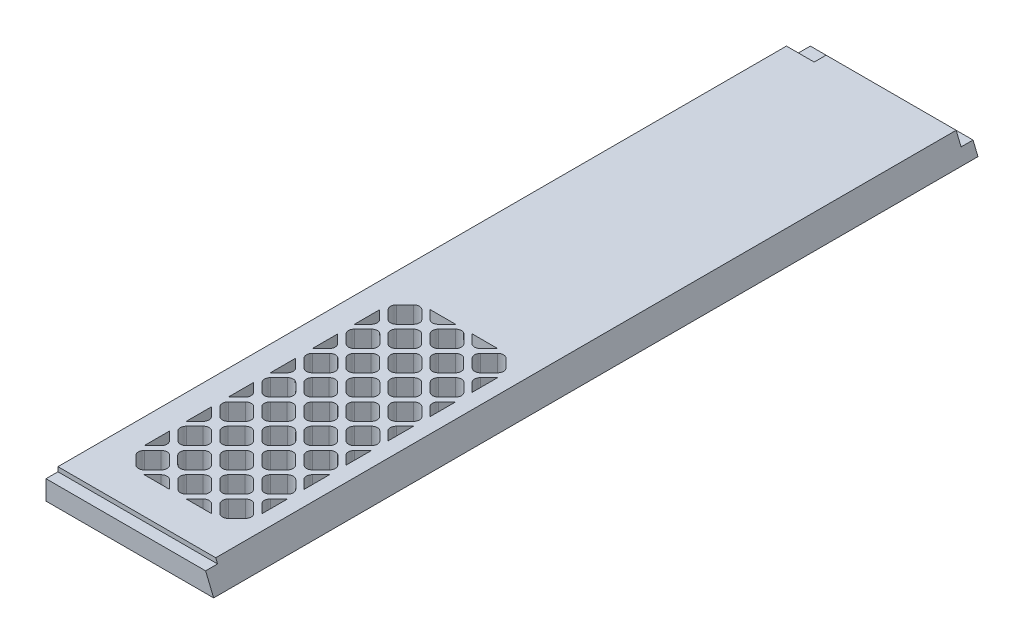
SolidWorks part; units mm, degrees
ref_plane "Front Plane" through (0, 0, 0) normal (0, 0, 1) x (1, 0, 0)
ref_plane "Top Plane" through (0, 0, 0) normal (0, 1, 0) x (1, 0, 0)
ref_plane "Right Plane" through (0, 0, 0) normal (1, 0, 0) x (0, 0, -1)
sketch "Sketch1" plane through (0, 0, 0) normal (0, 0, 1) x (1, 0, 0)
  line L0 (0, 0) -> (0, 12.7)
  line L1 (0, 12.7) -> (83.8935, 12.7)
  line L2 (83.8935, 12.7) -> (89.154, 0)
  line L3 (89.154, 0) -> (0, 0)
  dimension "D1" = 12.7
  dimension "D2" = 67.5
  dimension "D3" = 89.154
extrude "Boss-Extrude1" add sketch "Sketch1" along normal blind 406.4
sketch "Sketch2" plane through (0, 12.7, 0) normal (0, -1, 0) x (1, 0, 0)
  line L5 (89.154, 406.4) -> (89.154, 0) construction
  line L6 (0, 406.4) -> (89.154, 406.4)
  line L7 (0, 406.4) -> (0, 400.05)
  line L8 (0, 400.05) -> (89.154, 400.05)
  line L9 (89.154, 406.4) -> (89.154, 400.05)
  dimension "D1" = 6.35
extrude "Cut-Extrude1" cut sketch "Sketch2" along normal blind 2.3622
sketch "Sketch3" plane through (0, 0, 0) normal (0, -1, 0) x (1, 0, 0)
  line L0 (15.4898, 374.1011) -> (19.9799, 378.5912)
  line L1 (13.2447, 380.8363) -> (75.9093, 380.8363)
  line L2 (13.2447, 380.8363) -> (13.2447, 228.7637)
  line L3 (13.2447, 228.7637) -> (75.9093, 228.7637)
  line L4 (75.9093, 380.8363) -> (75.9093, 228.7637)
  line L5 (24.4701, 378.5912) -> (28.9602, 374.1011)
  line L6 (28.9602, 369.6109) -> (24.4701, 365.1208)
  line L7 (19.9799, 365.1208) -> (15.4898, 369.6109)
  line L8 (42.3319, 365.1208) -> (37.8418, 369.6109)
  line L9 (37.8418, 374.1011) -> (42.3319, 378.5912)
  line L10 (46.8221, 378.5912) -> (51.3122, 374.1011)
  line L11 (51.3122, 369.6109) -> (46.8221, 365.1208)
  line L12 (64.6839, 365.1208) -> (60.1938, 369.6109)
  line L13 (60.1938, 374.1011) -> (64.6839, 378.5912)
  line L14 (69.1741, 378.5912) -> (73.6642, 374.1011)
  line L15 (73.6642, 369.6109) -> (69.1741, 365.1208)
  line L16 (19.9799, 342.7688) -> (15.4898, 347.2589)
  line L17 (15.4898, 351.7491) -> (19.9799, 356.2392)
  line L18 (24.4701, 356.2392) -> (28.9602, 351.7491)
  line L19 (28.9602, 347.2589) -> (24.4701, 342.7688)
  line L20 (42.3319, 342.7688) -> (37.8418, 347.2589)
  line L21 (37.8418, 351.7491) -> (42.3319, 356.2392)
  line L22 (46.8221, 356.2392) -> (51.3122, 351.7491)
  line L23 (51.3122, 347.2589) -> (46.8221, 342.7688)
  line L24 (64.6839, 342.7688) -> (60.1938, 347.2589)
  line L25 (60.1938, 351.7491) -> (64.6839, 356.2392)
  line L26 (69.1741, 356.2392) -> (73.6642, 351.7491)
  line L27 (73.6642, 347.2589) -> (69.1741, 342.7688)
  line L28 (19.9799, 320.4168) -> (15.4898, 324.9069)
  line L29 (15.4898, 329.3971) -> (19.9799, 333.8872)
  line L30 (24.4701, 333.8872) -> (28.9602, 329.3971)
  line L31 (28.9602, 324.9069) -> (24.4701, 320.4168)
  line L32 (42.3319, 320.4168) -> (37.8418, 324.9069)
  line L33 (37.8418, 329.3971) -> (42.3319, 333.8872)
  line L34 (46.8221, 333.8872) -> (51.3122, 329.3971)
  line L35 (51.3122, 324.9069) -> (46.8221, 320.4168)
  line L36 (64.6839, 320.4168) -> (60.1938, 324.9069)
  line L37 (60.1938, 329.3971) -> (64.6839, 333.8872)
  line L38 (69.1741, 333.8872) -> (73.6642, 329.3971)
  line L39 (73.6642, 324.9069) -> (69.1741, 320.4168)
  line L40 (19.9799, 298.0648) -> (15.4898, 302.5549)
  line L41 (15.4898, 307.0451) -> (19.9799, 311.5352)
  line L42 (24.4701, 311.5352) -> (28.9602, 307.0451)
  line L43 (28.9602, 302.5549) -> (24.4701, 298.0648)
  line L44 (42.3319, 298.0648) -> (37.8418, 302.5549)
  line L45 (37.8418, 307.0451) -> (42.3319, 311.5352)
  line L46 (46.8221, 311.5352) -> (51.3122, 307.0451)
  line L47 (51.3122, 302.5549) -> (46.8221, 298.0648)
  line L48 (64.6839, 298.0648) -> (60.1938, 302.5549)
  line L49 (60.1938, 307.0451) -> (64.6839, 311.5352)
  line L50 (69.1741, 311.5352) -> (73.6642, 307.0451)
  line L51 (73.6642, 302.5549) -> (69.1741, 298.0648)
  line L52 (19.9799, 275.7128) -> (15.4898, 280.2029)
  line L53 (15.4898, 284.6931) -> (19.9799, 289.1832)
  line L54 (24.4701, 289.1832) -> (28.9602, 284.6931)
  line L55 (28.9602, 280.2029) -> (24.4701, 275.7128)
  line L56 (42.3319, 275.7128) -> (37.8418, 280.2029)
  line L57 (37.8418, 284.6931) -> (42.3319, 289.1832)
  line L58 (46.8221, 289.1832) -> (51.3122, 284.6931)
  line L59 (51.3122, 280.2029) -> (46.8221, 275.7128)
  line L60 (64.6839, 275.7128) -> (60.1938, 280.2029)
  line L61 (60.1938, 284.6931) -> (64.6839, 289.1832)
  line L62 (69.1741, 289.1832) -> (73.6642, 284.6931)
  line L63 (73.6642, 280.2029) -> (69.1741, 275.7128)
  line L64 (19.9799, 253.3608) -> (15.4898, 257.8509)
  line L65 (15.4898, 262.3411) -> (19.9799, 266.8312)
  line L66 (24.4701, 266.8312) -> (28.9602, 262.3411)
  line L67 (28.9602, 257.8509) -> (24.4701, 253.3608)
  line L68 (42.3319, 253.3608) -> (37.8418, 257.8509)
  line L69 (37.8418, 262.3411) -> (42.3319, 266.8312)
  line L70 (46.8221, 266.8312) -> (51.3122, 262.3411)
  line L71 (51.3122, 257.8509) -> (46.8221, 253.3608)
  line L72 (64.6839, 253.3608) -> (60.1938, 257.8509)
  line L73 (60.1938, 262.3411) -> (64.6839, 266.8312)
  line L74 (69.1741, 266.8312) -> (73.6642, 262.3411)
  line L75 (73.6642, 257.8509) -> (69.1741, 253.3608)
  line L76 (19.9799, 231.0088) -> (15.4898, 235.4989)
  line L77 (15.4898, 239.9891) -> (19.9799, 244.4792)
  line L78 (24.4701, 244.4792) -> (28.9602, 239.9891)
  line L79 (28.9602, 235.4989) -> (24.4701, 231.0088)
  line L80 (42.3319, 231.0088) -> (37.8418, 235.4989)
  line L81 (37.8418, 239.9891) -> (42.3319, 244.4792)
  line L82 (46.8221, 244.4792) -> (51.3122, 239.9891)
  line L83 (51.3122, 235.4989) -> (46.8221, 231.0088)
  line L84 (64.6839, 231.0088) -> (60.1938, 235.4989)
  line L85 (60.1938, 239.9891) -> (64.6839, 244.4792)
  line L86 (69.1741, 244.4792) -> (73.6642, 239.9891)
  line L87 (73.6642, 235.4989) -> (69.1741, 231.0088)
  line L91 (0, 400.05) -> (89.154, 400.05) construction
  line L92 (13.2447, 376.3461) -> (17.7349, 380.8363)
  line L98 (35.5967, 376.3461) -> (40.0869, 380.8363)
  line L99 (31.1066, 376.3461) -> (26.6165, 380.8363)
  line L102 (57.9487, 376.3461) -> (62.4389, 380.8363)
  line L103 (53.4586, 376.3461) -> (48.9685, 380.8363)
  line L107 (75.8106, 376.3461) -> (71.3205, 380.8363)
  line L108 (26.6165, 362.9744) -> (31.1066, 367.4645)
  line L109 (40.0869, 362.9744) -> (35.5967, 367.4645)
  line L110 (35.5967, 353.9941) -> (40.0869, 358.4843)
  line L111 (31.1066, 353.9941) -> (26.6165, 358.4843)
  line L112 (48.9685, 362.9744) -> (53.4586, 367.4645)
  line L113 (62.4389, 362.9744) -> (57.9487, 367.4645)
  line L114 (57.9487, 353.9941) -> (62.4389, 358.4843)
  line L115 (53.4586, 353.9941) -> (48.9685, 358.4843)
  line L116 (71.3205, 362.9744) -> (75.8106, 367.4645)
  line L119 (75.8106, 353.9941) -> (71.3205, 358.4843)
  line L120 (26.6165, 340.6224) -> (31.1066, 345.1125)
  line L121 (40.0869, 340.6224) -> (35.5967, 345.1125)
  line L122 (35.5967, 331.6421) -> (40.0869, 336.1323)
  line L123 (31.1066, 331.6421) -> (26.6165, 336.1323)
  line L124 (48.9685, 340.6224) -> (53.4586, 345.1125)
  line L125 (62.4389, 340.6224) -> (57.9487, 345.1125)
  line L126 (57.9487, 331.6421) -> (62.4389, 336.1323)
  line L127 (53.4586, 331.6421) -> (48.9685, 336.1323)
  line L128 (71.3205, 340.6224) -> (75.8106, 345.1125)
  line L131 (75.8106, 331.6421) -> (71.3205, 336.1323)
  line L132 (26.6165, 318.2704) -> (31.1066, 322.7605)
  line L133 (40.0869, 318.2704) -> (35.5967, 322.7605)
  line L134 (35.5967, 309.2901) -> (40.0869, 313.7803)
  line L135 (31.1066, 309.2901) -> (26.6165, 313.7803)
  line L136 (48.9685, 318.2704) -> (53.4586, 322.7605)
  line L137 (62.4389, 318.2704) -> (57.9487, 322.7605)
  line L138 (57.9487, 309.2901) -> (62.4389, 313.7803)
  line L139 (53.4586, 309.2901) -> (48.9685, 313.7803)
  line L140 (71.3205, 318.2704) -> (75.8106, 322.7605)
  line L143 (75.8106, 309.2901) -> (71.3205, 313.7803)
  line L144 (26.6165, 295.9184) -> (31.1066, 300.4085)
  line L145 (40.0869, 295.9184) -> (35.5967, 300.4085)
  line L146 (35.5967, 286.9381) -> (40.0869, 291.4283)
  line L147 (31.1066, 286.9381) -> (26.6165, 291.4283)
  line L148 (48.9685, 295.9184) -> (53.4586, 300.4085)
  line L149 (62.4389, 295.9184) -> (57.9487, 300.4085)
  line L150 (57.9487, 286.9381) -> (62.4389, 291.4283)
  line L151 (53.4586, 286.9381) -> (48.9685, 291.4283)
  line L152 (71.3205, 295.9184) -> (75.8106, 300.4085)
  line L155 (75.8106, 286.9381) -> (71.3205, 291.4283)
  line L156 (26.6165, 273.5664) -> (31.1066, 278.0565)
  line L157 (40.0869, 273.5664) -> (35.5967, 278.0565)
  line L158 (35.5967, 264.5861) -> (40.0869, 269.0763)
  line L159 (31.1066, 264.5861) -> (26.6165, 269.0763)
  line L160 (48.9685, 273.5664) -> (53.4586, 278.0565)
  line L161 (62.4389, 273.5664) -> (57.9487, 278.0565)
  line L162 (57.9487, 264.5861) -> (62.4389, 269.0763)
  line L163 (53.4586, 264.5861) -> (48.9685, 269.0763)
  line L164 (71.3205, 273.5664) -> (75.8106, 278.0565)
  line L167 (75.8106, 264.5861) -> (71.3205, 269.0763)
  line L168 (26.6165, 251.2144) -> (31.1066, 255.7045)
  line L169 (40.0869, 251.2144) -> (35.5967, 255.7045)
  line L170 (35.5967, 242.2341) -> (40.0869, 246.7243)
  line L171 (31.1066, 242.2341) -> (26.6165, 246.7243)
  line L172 (48.9685, 251.2144) -> (53.4586, 255.7045)
  line L173 (62.4389, 251.2144) -> (57.9487, 255.7045)
  line L174 (57.9487, 242.2341) -> (62.4389, 246.7243)
  line L175 (53.4586, 242.2341) -> (48.9685, 246.7243)
  line L176 (71.3205, 251.2144) -> (75.8106, 255.7045)
  line L179 (75.8106, 242.2341) -> (71.3205, 246.7243)
  line L180 (26.6165, 228.8624) -> (31.1066, 233.3525)
  line L181 (40.0869, 228.8624) -> (35.5967, 233.3525)
  line L184 (48.9685, 228.8624) -> (53.4586, 233.3525)
  line L185 (62.4389, 228.8624) -> (57.9487, 233.3525)
  line L188 (71.3205, 228.8624) -> (75.8106, 233.3525)
  line L193 (17.7349, 362.9744) -> (13.2447, 367.4645)
  line L194 (13.2447, 353.9941) -> (17.7349, 358.4843)
  line L197 (17.7349, 340.6224) -> (13.2447, 345.1125)
  line L198 (13.2447, 331.6421) -> (17.7349, 336.1323)
  line L201 (17.7349, 318.2704) -> (13.2447, 322.7605)
  line L202 (13.2447, 309.2901) -> (17.7349, 313.7803)
  line L205 (17.7349, 295.9184) -> (13.2447, 300.4085)
  line L206 (13.2447, 286.9381) -> (17.7349, 291.4283)
  line L209 (17.7349, 273.5664) -> (13.2447, 278.0565)
  line L210 (13.2447, 264.5861) -> (17.7349, 269.0763)
  line L213 (17.7349, 251.2144) -> (13.2447, 255.7045)
  line L214 (13.2447, 242.2341) -> (17.7349, 246.7243)
  line L217 (17.7349, 228.8624) -> (13.2447, 233.3525)
  line L220 (80.3007, 376.3461) -> (84.7909, 380.8363) [skipped]
  line L221 (80.3007, 353.9941) -> (84.7909, 358.4843) [skipped]
  line L222 (80.3007, 331.6421) -> (84.7909, 336.1323) [skipped]
  line L223 (80.3007, 309.2901) -> (84.7909, 313.7803) [skipped]
  line L224 (80.3007, 286.9381) -> (84.7909, 291.4283) [skipped]
  line L225 (80.3007, 264.5861) -> (84.7909, 269.0763) [skipped]
  line L226 (80.3007, 242.2341) -> (84.7909, 246.7243) [skipped]
  line L227 (80.3007, 219.8821) -> (84.7909, 224.3723) [skipped]
  line L228 (57.9487, 219.8821) -> (62.4389, 224.3723) [skipped]
  line L229 (35.5967, 219.8821) -> (40.0869, 224.3723) [skipped]
  line L230 (13.2447, 219.8821) -> (17.7349, 224.3723) [skipped]
  arc A0 (24.4701, 365.1208) -> (19.9799, 365.1208) centre (22.225, 367.3659) cw
  arc A1 (28.9602, 374.1011) -> (28.9602, 369.6109) centre (26.7151, 371.856) cw
  arc A2 (15.4898, 374.1011) -> (15.4898, 369.6109) centre (17.7349, 371.856) ccw
  arc A3 (19.9799, 378.5912) -> (24.4701, 378.5912) centre (22.225, 376.3461) cw
  arc A4 (37.8418, 374.1011) -> (37.8418, 369.6109) centre (40.0869, 371.856) ccw
  arc A5 (46.8221, 365.1208) -> (42.3319, 365.1208) centre (44.577, 367.3659) cw
  arc A6 (42.3319, 378.5912) -> (46.8221, 378.5912) centre (44.577, 376.3461) cw
  arc A7 (51.3122, 374.1011) -> (51.3122, 369.6109) centre (49.0671, 371.856) cw
  arc A8 (60.1938, 374.1011) -> (60.1938, 369.6109) centre (62.4389, 371.856) ccw
  arc A9 (69.1741, 365.1208) -> (64.6839, 365.1208) centre (66.929, 367.3659) cw
  arc A10 (64.6839, 378.5912) -> (69.1741, 378.5912) centre (66.929, 376.3461) cw
  arc A11 (73.6642, 374.1011) -> (73.6642, 369.6109) centre (71.4191, 371.856) cw
  arc A12 (15.4898, 351.7491) -> (15.4898, 347.2589) centre (17.7349, 349.504) ccw
  arc A13 (24.4701, 342.7688) -> (19.9799, 342.7688) centre (22.225, 345.0139) cw
  arc A14 (19.9799, 356.2392) -> (24.4701, 356.2392) centre (22.225, 353.9941) cw
  arc A15 (28.9602, 351.7491) -> (28.9602, 347.2589) centre (26.7151, 349.504) cw
  arc A16 (37.8418, 351.7491) -> (37.8418, 347.2589) centre (40.0869, 349.504) ccw
  arc A17 (42.3319, 356.2392) -> (46.8221, 356.2392) centre (44.577, 353.9941) cw
  arc A18 (51.3122, 351.7491) -> (51.3122, 347.2589) centre (49.0671, 349.504) cw
  arc A19 (46.8221, 342.7688) -> (42.3319, 342.7688) centre (44.577, 345.0139) cw
  arc A20 (60.1938, 351.7491) -> (60.1938, 347.2589) centre (62.4389, 349.504) ccw
  arc A21 (64.6839, 356.2392) -> (69.1741, 356.2392) centre (66.929, 353.9941) cw
  arc A22 (73.6642, 351.7491) -> (73.6642, 347.2589) centre (71.4191, 349.504) cw
  arc A23 (69.1741, 342.7688) -> (64.6839, 342.7688) centre (66.929, 345.0139) cw
  arc A24 (15.4898, 329.3971) -> (15.4898, 324.9069) centre (17.7349, 327.152) ccw
  arc A25 (24.4701, 320.4168) -> (19.9799, 320.4168) centre (22.225, 322.6619) cw
  arc A26 (19.9799, 333.8872) -> (24.4701, 333.8872) centre (22.225, 331.6421) cw
  arc A27 (28.9602, 329.3971) -> (28.9602, 324.9069) centre (26.7151, 327.152) cw
  arc A28 (37.8418, 329.3971) -> (37.8418, 324.9069) centre (40.0869, 327.152) ccw
  arc A29 (42.3319, 333.8872) -> (46.8221, 333.8872) centre (44.577, 331.6421) cw
  arc A30 (51.3122, 329.3971) -> (51.3122, 324.9069) centre (49.0671, 327.152) cw
  arc A31 (46.8221, 320.4168) -> (42.3319, 320.4168) centre (44.577, 322.6619) cw
  arc A32 (60.1938, 329.3971) -> (60.1938, 324.9069) centre (62.4389, 327.152) ccw
  arc A33 (64.6839, 333.8872) -> (69.1741, 333.8872) centre (66.929, 331.6421) cw
  arc A34 (73.6642, 329.3971) -> (73.6642, 324.9069) centre (71.4191, 327.152) cw
  arc A35 (69.1741, 320.4168) -> (64.6839, 320.4168) centre (66.929, 322.6619) cw
  arc A36 (15.4898, 307.0451) -> (15.4898, 302.5549) centre (17.7349, 304.8) ccw
  arc A37 (24.4701, 298.0648) -> (19.9799, 298.0648) centre (22.225, 300.3099) cw
  arc A38 (19.9799, 311.5352) -> (24.4701, 311.5352) centre (22.225, 309.2901) cw
  arc A39 (28.9602, 307.0451) -> (28.9602, 302.5549) centre (26.7151, 304.8) cw
  arc A40 (37.8418, 307.0451) -> (37.8418, 302.5549) centre (40.0869, 304.8) ccw
  arc A41 (42.3319, 311.5352) -> (46.8221, 311.5352) centre (44.577, 309.2901) cw
  arc A42 (51.3122, 307.0451) -> (51.3122, 302.5549) centre (49.0671, 304.8) cw
  arc A43 (46.8221, 298.0648) -> (42.3319, 298.0648) centre (44.577, 300.3099) cw
  arc A44 (60.1938, 307.0451) -> (60.1938, 302.5549) centre (62.4389, 304.8) ccw
  arc A45 (64.6839, 311.5352) -> (69.1741, 311.5352) centre (66.929, 309.2901) cw
  arc A46 (73.6642, 307.0451) -> (73.6642, 302.5549) centre (71.4191, 304.8) cw
  arc A47 (69.1741, 298.0648) -> (64.6839, 298.0648) centre (66.929, 300.3099) cw
  arc A48 (15.4898, 284.6931) -> (15.4898, 280.2029) centre (17.7349, 282.448) ccw
  arc A49 (24.4701, 275.7128) -> (19.9799, 275.7128) centre (22.225, 277.9579) cw
  arc A50 (19.9799, 289.1832) -> (24.4701, 289.1832) centre (22.225, 286.9381) cw
  arc A51 (28.9602, 284.6931) -> (28.9602, 280.2029) centre (26.7151, 282.448) cw
  arc A52 (37.8418, 284.6931) -> (37.8418, 280.2029) centre (40.0869, 282.448) ccw
  arc A53 (42.3319, 289.1832) -> (46.8221, 289.1832) centre (44.577, 286.9381) cw
  arc A54 (51.3122, 284.6931) -> (51.3122, 280.2029) centre (49.0671, 282.448) cw
  arc A55 (46.8221, 275.7128) -> (42.3319, 275.7128) centre (44.577, 277.9579) cw
  arc A56 (60.1938, 284.6931) -> (60.1938, 280.2029) centre (62.4389, 282.448) ccw
  arc A57 (64.6839, 289.1832) -> (69.1741, 289.1832) centre (66.929, 286.9381) cw
  arc A58 (73.6642, 284.6931) -> (73.6642, 280.2029) centre (71.4191, 282.448) cw
  arc A59 (69.1741, 275.7128) -> (64.6839, 275.7128) centre (66.929, 277.9579) cw
  arc A60 (15.4898, 262.3411) -> (15.4898, 257.8509) centre (17.7349, 260.096) ccw
  arc A61 (24.4701, 253.3608) -> (19.9799, 253.3608) centre (22.225, 255.6059) cw
  arc A62 (19.9799, 266.8312) -> (24.4701, 266.8312) centre (22.225, 264.5861) cw
  arc A63 (28.9602, 262.3411) -> (28.9602, 257.8509) centre (26.7151, 260.096) cw
  arc A64 (37.8418, 262.3411) -> (37.8418, 257.8509) centre (40.0869, 260.096) ccw
  arc A65 (42.3319, 266.8312) -> (46.8221, 266.8312) centre (44.577, 264.5861) cw
  arc A66 (51.3122, 262.3411) -> (51.3122, 257.8509) centre (49.0671, 260.096) cw
  arc A67 (46.8221, 253.3608) -> (42.3319, 253.3608) centre (44.577, 255.6059) cw
  arc A68 (60.1938, 262.3411) -> (60.1938, 257.8509) centre (62.4389, 260.096) ccw
  arc A69 (64.6839, 266.8312) -> (69.1741, 266.8312) centre (66.929, 264.5861) cw
  arc A70 (73.6642, 262.3411) -> (73.6642, 257.8509) centre (71.4191, 260.096) cw
  arc A71 (69.1741, 253.3608) -> (64.6839, 253.3608) centre (66.929, 255.6059) cw
  arc A72 (15.4898, 239.9891) -> (15.4898, 235.4989) centre (17.7349, 237.744) ccw
  arc A73 (24.4701, 231.0088) -> (19.9799, 231.0088) centre (22.225, 233.2539) cw
  arc A74 (19.9799, 244.4792) -> (24.4701, 244.4792) centre (22.225, 242.2341) cw
  arc A75 (28.9602, 239.9891) -> (28.9602, 235.4989) centre (26.7151, 237.744) cw
  arc A76 (37.8418, 239.9891) -> (37.8418, 235.4989) centre (40.0869, 237.744) ccw
  arc A77 (42.3319, 244.4792) -> (46.8221, 244.4792) centre (44.577, 242.2341) cw
  arc A78 (51.3122, 239.9891) -> (51.3122, 235.4989) centre (49.0671, 237.744) cw
  arc A79 (46.8221, 231.0088) -> (42.3319, 231.0088) centre (44.577, 233.2539) cw
  arc A80 (60.1938, 239.9891) -> (60.1938, 235.4989) centre (62.4389, 237.744) ccw
  arc A81 (64.6839, 244.4792) -> (69.1741, 244.4792) centre (66.929, 242.2341) cw
  arc A82 (73.6642, 239.9891) -> (73.6642, 235.4989) centre (71.4191, 237.744) cw
  arc A83 (69.1741, 231.0088) -> (64.6839, 231.0088) centre (66.929, 233.2539) cw
  arc A91 (35.5967, 376.3461) -> (31.1066, 376.3461) centre (33.3517, 378.5912) cw
  arc A95 (57.9487, 376.3461) -> (53.4586, 376.3461) centre (55.7037, 378.5912) cw
  arc A99 (75.9093, 376.2516) -> (75.8106, 376.3461) centre (78.0557, 378.5912) cw
  arc A100 (35.5967, 367.4645) -> (31.1066, 367.4645) centre (33.3517, 365.2194) ccw
  arc A101 (26.6165, 358.4843) -> (26.6165, 362.9744) centre (28.8616, 360.7293) cw
  arc A102 (40.0869, 358.4843) -> (40.0869, 362.9744) centre (37.8418, 360.7293) ccw
  arc A103 (35.5967, 353.9941) -> (31.1066, 353.9941) centre (33.3517, 356.2392) cw
  arc A104 (57.9487, 367.4645) -> (53.4586, 367.4645) centre (55.7037, 365.2194) ccw
  arc A105 (48.9685, 358.4843) -> (48.9685, 362.9744) centre (51.2136, 360.7293) cw
  arc A106 (62.4389, 358.4843) -> (62.4389, 362.9744) centre (60.1938, 360.7293) ccw
  arc A107 (57.9487, 353.9941) -> (53.4586, 353.9941) centre (55.7037, 356.2392) cw
  arc A108 (75.9093, 367.559) -> (75.8106, 367.4645) centre (78.0557, 365.2194) ccw
  arc A109 (71.3205, 358.4843) -> (71.3205, 362.9744) centre (73.5656, 360.7293) cw
  arc A111 (75.9093, 353.8996) -> (75.8106, 353.9941) centre (78.0557, 356.2392) cw
  arc A112 (35.5967, 345.1125) -> (31.1066, 345.1125) centre (33.3517, 342.8674) ccw
  arc A113 (26.6165, 336.1323) -> (26.6165, 340.6224) centre (28.8616, 338.3773) cw
  arc A114 (40.0869, 336.1323) -> (40.0869, 340.6224) centre (37.8418, 338.3773) ccw
  arc A115 (35.5967, 331.6421) -> (31.1066, 331.6421) centre (33.3517, 333.8872) cw
  arc A116 (57.9487, 345.1125) -> (53.4586, 345.1125) centre (55.7037, 342.8674) ccw
  arc A117 (48.9685, 336.1323) -> (48.9685, 340.6224) centre (51.2136, 338.3773) cw
  arc A118 (62.4389, 336.1323) -> (62.4389, 340.6224) centre (60.1938, 338.3773) ccw
  arc A119 (57.9487, 331.6421) -> (53.4586, 331.6421) centre (55.7037, 333.8872) cw
  arc A120 (75.9093, 345.207) -> (75.8106, 345.1125) centre (78.0557, 342.8674) ccw
  arc A121 (71.3205, 336.1323) -> (71.3205, 340.6224) centre (73.5656, 338.3773) cw
  arc A123 (75.9093, 331.5476) -> (75.8106, 331.6421) centre (78.0557, 333.8872) cw
  arc A124 (35.5967, 322.7605) -> (31.1066, 322.7605) centre (33.3517, 320.5154) ccw
  arc A125 (26.6165, 313.7803) -> (26.6165, 318.2704) centre (28.8616, 316.0253) cw
  arc A126 (40.0869, 313.7803) -> (40.0869, 318.2704) centre (37.8418, 316.0253) ccw
  arc A127 (35.5967, 309.2901) -> (31.1066, 309.2901) centre (33.3517, 311.5352) cw
  arc A128 (57.9487, 322.7605) -> (53.4586, 322.7605) centre (55.7037, 320.5154) ccw
  arc A129 (48.9685, 313.7803) -> (48.9685, 318.2704) centre (51.2136, 316.0253) cw
  arc A130 (62.4389, 313.7803) -> (62.4389, 318.2704) centre (60.1938, 316.0253) ccw
  arc A131 (57.9487, 309.2901) -> (53.4586, 309.2901) centre (55.7037, 311.5352) cw
  arc A132 (75.9093, 322.855) -> (75.8106, 322.7605) centre (78.0557, 320.5154) ccw
  arc A133 (71.3205, 313.7803) -> (71.3205, 318.2704) centre (73.5656, 316.0253) cw
  arc A135 (75.9093, 309.1956) -> (75.8106, 309.2901) centre (78.0557, 311.5352) cw
  arc A136 (35.5967, 300.4085) -> (31.1066, 300.4085) centre (33.3517, 298.1634) ccw
  arc A137 (26.6165, 291.4283) -> (26.6165, 295.9184) centre (28.8616, 293.6733) cw
  arc A138 (40.0869, 291.4283) -> (40.0869, 295.9184) centre (37.8418, 293.6733) ccw
  arc A139 (35.5967, 286.9381) -> (31.1066, 286.9381) centre (33.3517, 289.1832) cw
  arc A140 (57.9487, 300.4085) -> (53.4586, 300.4085) centre (55.7037, 298.1634) ccw
  arc A141 (48.9685, 291.4283) -> (48.9685, 295.9184) centre (51.2136, 293.6733) cw
  arc A142 (62.4389, 291.4283) -> (62.4389, 295.9184) centre (60.1938, 293.6733) ccw
  arc A143 (57.9487, 286.9381) -> (53.4586, 286.9381) centre (55.7037, 289.1832) cw
  arc A144 (75.9093, 300.503) -> (75.8106, 300.4085) centre (78.0557, 298.1634) ccw
  arc A145 (71.3205, 291.4283) -> (71.3205, 295.9184) centre (73.5656, 293.6733) cw
  arc A147 (75.9093, 286.8436) -> (75.8106, 286.9381) centre (78.0557, 289.1832) cw
  arc A148 (35.5967, 278.0565) -> (31.1066, 278.0565) centre (33.3517, 275.8114) ccw
  arc A149 (26.6165, 269.0763) -> (26.6165, 273.5664) centre (28.8616, 271.3213) cw
  arc A150 (40.0869, 269.0763) -> (40.0869, 273.5664) centre (37.8418, 271.3213) ccw
  arc A151 (35.5967, 264.5861) -> (31.1066, 264.5861) centre (33.3517, 266.8312) cw
  arc A152 (57.9487, 278.0565) -> (53.4586, 278.0565) centre (55.7037, 275.8114) ccw
  arc A153 (48.9685, 269.0763) -> (48.9685, 273.5664) centre (51.2136, 271.3213) cw
  arc A154 (62.4389, 269.0763) -> (62.4389, 273.5664) centre (60.1938, 271.3213) ccw
  arc A155 (57.9487, 264.5861) -> (53.4586, 264.5861) centre (55.7037, 266.8312) cw
  arc A156 (75.9093, 278.151) -> (75.8106, 278.0565) centre (78.0557, 275.8114) ccw
  arc A157 (71.3205, 269.0763) -> (71.3205, 273.5664) centre (73.5656, 271.3213) cw
  arc A159 (75.9093, 264.4916) -> (75.8106, 264.5861) centre (78.0557, 266.8312) cw
  arc A160 (35.5967, 255.7045) -> (31.1066, 255.7045) centre (33.3517, 253.4594) ccw
  arc A161 (26.6165, 246.7243) -> (26.6165, 251.2144) centre (28.8616, 248.9693) cw
  arc A162 (40.0869, 246.7243) -> (40.0869, 251.2144) centre (37.8418, 248.9693) ccw
  arc A163 (35.5967, 242.2341) -> (31.1066, 242.2341) centre (33.3517, 244.4792) cw
  arc A164 (57.9487, 255.7045) -> (53.4586, 255.7045) centre (55.7037, 253.4594) ccw
  arc A165 (48.9685, 246.7243) -> (48.9685, 251.2144) centre (51.2136, 248.9693) cw
  arc A166 (62.4389, 246.7243) -> (62.4389, 251.2144) centre (60.1938, 248.9693) ccw
  arc A167 (57.9487, 242.2341) -> (53.4586, 242.2341) centre (55.7037, 244.4792) cw
  arc A168 (75.9093, 255.799) -> (75.8106, 255.7045) centre (78.0557, 253.4594) ccw
  arc A169 (71.3205, 246.7243) -> (71.3205, 251.2144) centre (73.5656, 248.9693) cw
  arc A171 (75.9093, 242.1396) -> (75.8106, 242.2341) centre (78.0557, 244.4792) cw
  arc A172 (35.5967, 233.3525) -> (31.1066, 233.3525) centre (33.3517, 231.1074) ccw
  arc A173 (26.522, 228.7637) -> (26.6165, 228.8624) centre (28.8616, 226.6173) cw
  arc A174 (40.1814, 228.7637) -> (40.0869, 228.8624) centre (37.8418, 226.6173) ccw
  arc A176 (57.9487, 233.3525) -> (53.4586, 233.3525) centre (55.7037, 231.1074) ccw
  arc A177 (48.874, 228.7637) -> (48.9685, 228.8624) centre (51.2136, 226.6173) cw
  arc A178 (62.5334, 228.7637) -> (62.4389, 228.8624) centre (60.1938, 226.6173) ccw
  arc A180 (75.9093, 233.447) -> (75.8106, 233.3525) centre (78.0557, 231.1074) ccw
  arc A181 (71.226, 228.7637) -> (71.3205, 228.8624) centre (73.5656, 226.6173) cw
  arc A186 (17.7349, 358.4843) -> (17.7349, 362.9744) centre (15.4898, 360.7293) ccw
  arc A190 (17.7349, 336.1323) -> (17.7349, 340.6224) centre (15.4898, 338.3773) ccw
  arc A194 (17.7349, 313.7803) -> (17.7349, 318.2704) centre (15.4898, 316.0253) ccw
  arc A198 (17.7349, 291.4283) -> (17.7349, 295.9184) centre (15.4898, 293.6733) ccw
  arc A202 (17.7349, 269.0763) -> (17.7349, 273.5664) centre (15.4898, 271.3213) ccw
  arc A206 (17.7349, 246.7243) -> (17.7349, 251.2144) centre (15.4898, 248.9693) ccw
  arc A210 (17.8294, 228.7637) -> (17.7349, 228.8624) centre (15.4898, 226.6173) ccw
  point P11 (22.225, 362.8757)
  point P16 (13.2447, 371.856)
  point P19 (22.225, 380.8363)
  point P44 (44.577, 380.8363)
  point P45 (13.2447, 304.8)
  point P272 (44.577, 400.05)
  point P281 (10.9997, 374.1011)
  point P284 (2.0194, 383.0813)
  point P287 (10.9997, 392.0616)
  dimension "D4" = 3.175
  dimension "D1" = 12.7
  dimension "D2" = 45
  dimension "D3" = 12.7
  dimension "D8" = 12.7
  dimension "D9" = 12.7
  dimension "D10" = 3.175
  dimension "D5" = 3
  dimension "D7" = 7
extrude "Cut-Extrude3" cut sketch "Sketch3" against normal through all contours A3 L0 A2 L7 A0 L6 A1 L5 | A7 L10 A6 L9 A4 L8 A5 L11 | A11 L14 A10 L13 A8 L12 A9 L15 | A91 L98 L1 L99 | L194 A186 L193 L2 | A103 L110 A102 L109 A100 L108 A101 L111 | A107 L114 A106 L113 A104 L112 A105 L115 | A111 L4 A108 L116 A109 L119 | A15 L18 A14 L17 A12 L16 A13 L19 | A19 L23 A18 L22 A17 L21 A16 L20 | A23 L27 A22 L26 A21 L25 A20 L24 | A123 L4 A120 L128 A121 L131 | A119 L126 A118 L125 A116 L124 A117 L127 | A115 L122 A114 L121 A112 L120 A113 L123 | L198 A190 L197 L2 | A27 L30 A26 L29 A24 L28 A25 L31 | A31 L35 A30 L34 A29 L33 A28 L32 | A35 L39 A34 L38 A33 L37 A32 L36 | A131 L138 A130 L137 A128 L136 A129 L139 | A135 L4 A132 L140 A133 L143 | A95 L102 L1 L103 | A127 L134 A126 L133 A124 L132 A125 L135 | L202 A194 L201 L2 | A39 L42 A38 L41 A36 L40 A37 L43 | A43 L47 A42 L46 A41 L45 A40 L44 | A47 L51 A46 L50 A45 L49 A44 L48 | L206 A198 L205 L2 | A51 L54 A50 L53 A48 L52 A49 L55 | A139 L146 A138 L145 A136 L144 A137 L147 | A55 L59 A54 L58 A53 L57 A52 L56 | A143 L150 A142 L149 A140 L148 A141 L151 | A147 L4 A144 L152 A145 L155 | A59 L63 A58 L62 A57 L61 A56 L60 | L210 A202 L209 L2 | A151 L158 A150 L157 A148 L156 A149 L159 | A155 L162 A154 L161 A152 L160 A153 L163 | A159 L4 A156 L164 A157 L167 | A71 L75 A70 L74 A69 L73 A68 L72 | A67 L71 A66 L70 A65 L69 A64 L68 | A63 L66 A62 L65 A60 L64 A61 L67 | L214 A206 L213 L2 | A75 L78 A74 L77 A72 L76 A73 L79 | A163 L170 A162 L169 A160 L168 A161 L171 | L3 A174 L181 A172 L180 A173 | A79 L83 A78 L82 A77 L81 A76 L80 | A167 L174 A166 L173 A164 L172 A165 L175 | A171 L4 A168 L176 A169 L179 | A83 L87 A82 L86 A81 L85 A80 L84 | L3 A178 L185 A176 L184 A177
sketch "Sketch4" plane through (0, 12.7, 0) normal (0, 1, 0) x (1, 0, 0)
  line L1 (126.762, -6.35) -> (14.7435, -6.35)
  line L2 (126.762, -6.35) -> (126.762, 0)
  line L3 (126.762, 0) -> (0, 0)
  line L4 (0, -6.35) -> (0, 0)
  line L6 (0, -6.35) -> (0, -12.7)
  line L7 (0, -12.7) -> (14.7435, -12.7)
  line L8 (14.7435, -6.35) -> (14.7435, -12.7)
  dimension "D1" = 6.35
  dimension "D2" = 6.35
extrude "Cut-Extrude4" cut sketch "Sketch4" against normal blind 6.35
